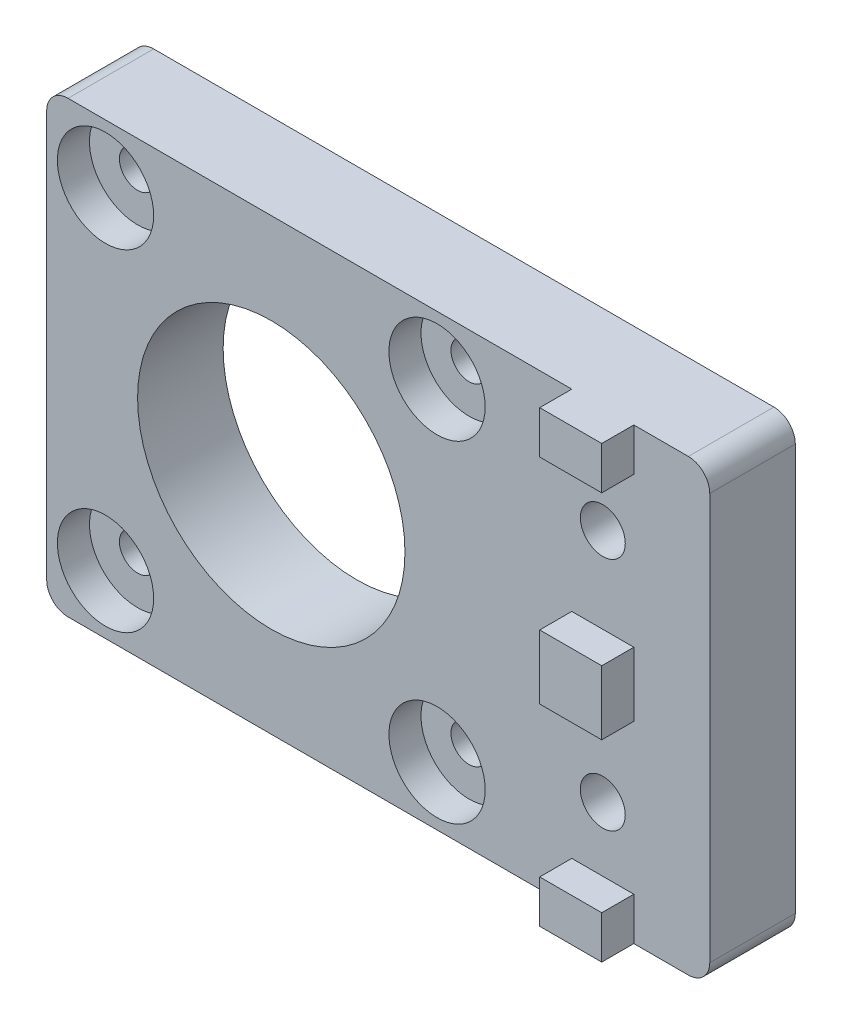
SolidWorks part; units mm, degrees
ref_plane "Plan de face" through (0, 0, 0) normal (0, 0, 1) x (1, 0, 0)
ref_plane "Plan de dessus" through (0, 0, 0) normal (0, 1, 0) x (1, 0, 0)
ref_plane "Plan de droite" through (0, 0, 0) normal (1, 0, 0) x (0, 0, -1)
sketch "Esquisse1" plane through (0, 0, 0) normal (0, 0, 1) x (1, 0, 0)
  line L1 (-31, 21) -> (31, 21)
  line L2 (-31, 21) -> (-31, -21)
  line L3 (-31, -21) -> (31, -21)
  line L4 (31, 21) -> (31, -21)
  dimension "D1" = 42
  dimension "D2" = 62
  dimension "D3" = 31
  dimension "D4" = 21
extrude "Boss.-Extru.1" add sketch "Esquisse1" along normal blind 8
sketch "Esquisse2" plane through (0, 0, 8) normal (0, 0, 1) x (1, 0, 0)
  line L0 (31, -21) -> (31, 21) construction
  line L1 (-31, -21) -> (31, -21) construction
  line L2 (31, 21) -> (-31, 21) construction
  line L3 (-31, 21) -> (-31, -21) construction
  circle A0 centre (21, 11) radius 2.1
  circle A1 centre (21, -11) radius 2.1
  circle A2 centre (-10, 0) radius 12.5
  circle A3 centre (-25.5, 15.5) radius 1.7
  circle A4 centre (5.5, 15.5) radius 1.7
  circle A5 centre (5.5, -15.5) radius 1.7
  circle A6 centre (-25.5, -15.5) radius 1.7
  dimension "D1" = 4.2
  dimension "D2" = 4.2
  dimension "D7" = 25
  dimension "D10" = 3.4
  dimension "D11" = 3.4
  dimension "D12" = 3.4
  dimension "D13" = 3.4
  dimension "D3" = 10
  dimension "D4" = 10
  dimension "D5" = 10
  dimension "D6" = 10
  dimension "D8" = 21
  dimension "D9" = 21
  dimension "D14" = 5.5
  dimension "D15" = 5.5
  dimension "D16" = 5.5
  dimension "D17" = 5.5
  dimension "D18" = 5.5
  dimension "D19" = 5.5
  dimension "D20" = 31
  dimension "D21" = 31
extrude "Enlèv. mat.-Extru.1" cut sketch "Esquisse2" against normal through all
sketch "Esquisse3" plane through (0, 0, 8) normal (0, 0, 1) x (1, 0, 0)
  line L0 (31, 21) -> (-31, 21) construction
  line L1 (18.1, 21) -> (23.9, 21)
  line L2 (18.1, 21) -> (18.1, 17)
  line L3 (18.1, 17) -> (23.9, 17)
  line L4 (23.9, 21) -> (23.9, 17)
  line L5 (-31, -21) -> (31, -21) construction
  line L6 (18.1, -21) -> (23.9, -21)
  line L7 (18.1, -21) -> (18.1, -17)
  line L8 (18.1, -17) -> (23.9, -17)
  line L9 (23.9, -21) -> (23.9, -17)
  line L10 (31, -21) -> (31, 21) construction
  line L11 (18.1, -3) -> (23.9, -3)
  line L12 (18.1, -3) -> (18.1, 3)
  line L13 (18.1, 3) -> (23.9, 3)
  line L14 (23.9, -3) -> (23.9, 3)
  dimension "D1" = 5.8
  dimension "D2" = 7.1
  dimension "D3" = 4
  dimension "D4" = 4
  dimension "D5" = 6
  dimension "D6" = 18
extrude "Boss.-Extru.2" add sketch "Esquisse3" along normal blind 3
fillet "Congé1" radius 2 4 edges at (-31, 21, 4) (-31, -21, 4) (31, 21, 4) (31, -21, 4)
sketch "Esquisse4" plane through (0, 0, 8) normal (0, 0, 1) x (1, 0, 0)
  circle A0 centre (-25.5, 15.5) radius 4.5
  circle A1 centre (-25.5, -15.5) radius 4.5
  circle A2 centre (5.5, -15.5) radius 4.5
  circle A3 centre (5.5, 15.5) radius 4.5
  dimension "D1" = 9
extrude "Enlèv. mat.-Extru.2" cut sketch "Esquisse4" against normal blind 3
